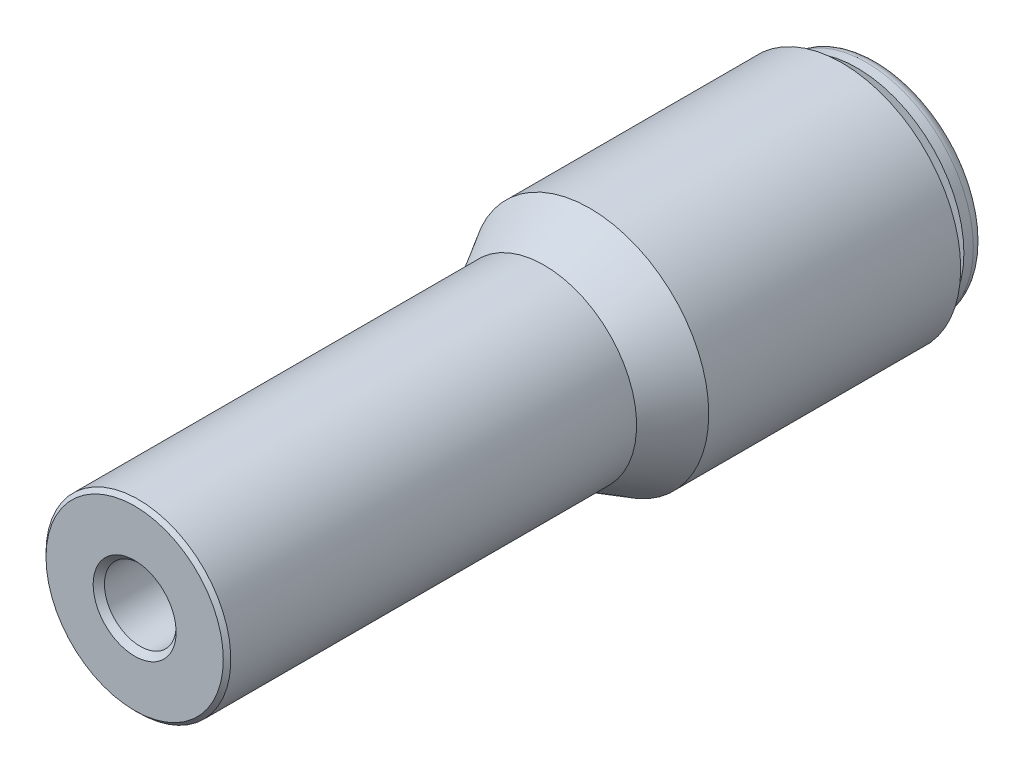
SolidWorks part; units mm, degrees
ref_plane "Front Plane" through (0, 0, 0) normal (0, 0, 1) x (1, 0, 0)
ref_plane "Top Plane" through (0, 0, 0) normal (0, 1, 0) x (1, 0, 0)
ref_plane "Right Plane" through (0, 0, 0) normal (1, 0, 0) x (0, 0, -1)
sketch "Sketch1" plane through (0, 0, 0) normal (1, 0, 0) x (0, 0, -1)
  line L0 (23.622, 7.2009) -> (24.257, 7.2009)
  line L1 (5.6395, 8.001) -> (22.606, 8.001)
  line L2 (4.0499, 3.175) -> (4.0499, 2.413)
  line L3 (4.0499, 3.175) -> (24.638, 3.175)
  line L4 (25.019, 6.4389) -> (25.019, 3.556)
  line L5 (4.0499, 2.413) -> (-25.019, 2.413)
  line L6 (22.606, 8.001) -> (22.606, 6.4808)
  line L7 (22.606, 6.4808) -> (23.622, 6.4808)
  line L8 (23.622, 7.2009) -> (23.622, 6.4808)
  line L10 (0, 0) -> (25.019, 0) construction
  line L11 (-25.019, 6.35) -> (-25.019, 2.413)
  line L12 (24.638, 3.175) -> (25.019, 3.556)
  line L13 (0, 0) -> (0, 2.413) construction
  line L14 (-25.019, 6.35) -> (2.7799, 6.35)
  line L15 (2.7799, 6.35) -> (5.6395, 8.001)
  arc A0 (24.257, 7.2009) -> (25.019, 6.4389) centre (24.257, 6.4389) cw
  point P0 (0.127, 0)
  point P1 (25.019, 3.175)
  point P20 (25.019, 7.2009)
  dimension "D4" = 0.762
  dimension "D1" = 1.397
  dimension "D2" = 1.016
  dimension "D3" = 12.9616
  dimension "D6" = 14.4018
  dimension "D9" = 30
  dimension "D5" = 22.2391
  dimension "D8" = 0.762
  dimension "D11" = 25.019
  dimension "D10" = 1.27
revolve "Revolve1" add sketch "Sketch1" angle 360 about L10
chamfer "Chamfer1" distance 0.381 angle 45 2 edges at (6.35, 0, 25.019) (2.413, 0, 25.019)
sketch "Sketch2" plane through (0, 0, 25.019) normal (0, 0, 1) x (1, 0, 0)
  circle A0 centre (0, 0) radius 6.35 construction
  circle A1 centre (0, 0) radius 5.969
  circle A2 centre (0, 0) radius 5.969
  circle A3 centre (0, 0) radius 6.35
  circle A4 centre (0, 0) radius 6.223
  dimension "D2" = 12.446
  dimension "D1" = 0
extrude "Cut-Extrude1" cut sketch "Sketch2" against normal up to surface (27.7989 mm away) contours A3 A4 up to face at (6.35, 0, -2.7799)
equation "\"D6@Sketch1\" = \"G@Sketch1\"*.9"
equation "\"D3@Sketch1\" = \"D6@Sketch1\"*.9"
equation "\"D5@Sketch1\" = \"L@Sketch1\"/2.25"
equation "\"D11@Sketch1\" = \"L@Sketch1\"/2"
